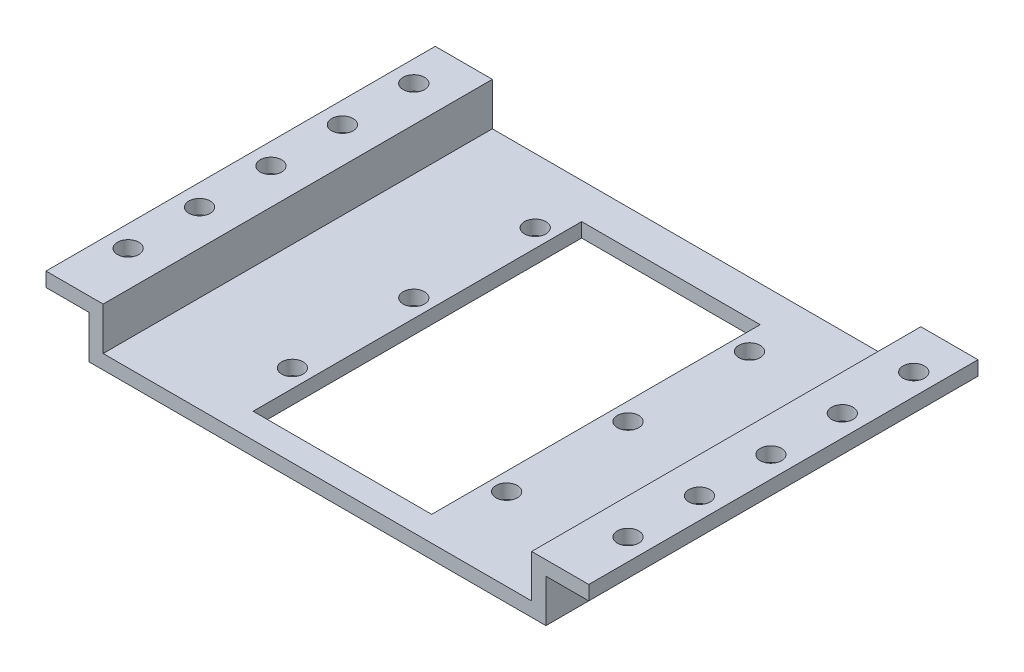
SolidWorks part; units mm, degrees
material "Polyetheretherketone (PEEK)"
ref_plane "Front Plane" through (0, 0, 0) normal (0, 0, 1) x (1, 0, 0)
ref_plane "Top Plane" through (0, 0, 0) normal (0, 1, 0) x (1, 0, 0)
ref_plane "Right Plane" through (0, 0, 0) normal (1, 0, 0) x (0, 0, -1)
sketch "Sketch1" plane through (0, 0, 0) normal (0, 0, 1) x (1, 0, 0)
  line L0 (0, 0) -> (0, 19.6061) construction
  line L1 (12.5, 0) -> (12.5, 2)
  line L2 (32, 0) -> (12.5, 0)
  line L3 (-12.5, 2) -> (-30, 2)
  line L4 (-30, 2) -> (-30, 8)
  line L5 (-30, 8) -> (-38, 8)
  line L6 (-38, 8) -> (-38, 6)
  line L7 (-38, 6) -> (-32, 6)
  line L8 (-32, 6) -> (-32, 0)
  line L9 (-32, 0) -> (-12.5, 0)
  line L10 (-12.5, 0) -> (-12.5, 2)
  line L11 (32, 6) -> (32, 0)
  line L12 (38, 6) -> (32, 6)
  line L13 (38, 8) -> (38, 6)
  line L14 (30, 8) -> (38, 8)
  line L15 (30, 2) -> (30, 8)
  line L16 (12.5, 2) -> (30, 2)
  dimension "D1" = 2
  dimension "D2" = 2
  dimension "D3" = 2
  dimension "D6" = 25
  dimension "D8" = 60
  dimension "D9" = 8
  dimension "D10" = 8
extrude "Boss-Extrude1" add sketch "Sketch1" along normal blind 50
sketch "Sketch2" plane through (0, 2, 0) normal (0, 1, 0) x (1, 0, 0)
  line L0 (-12.5, -50) -> (-30, -50) construction
  line L2 (0, 0) -> (0, -23.6531) construction
  point P0 (-15, -47)
  point P5 (-15, -30)
  point P6 (15, -13)
  point P7 (-15, -13)
  point P8 (15, -30)
  point P12 (15, -47)
  dimension "D1" = 3
  dimension "D2" = 30
  dimension "D3" = 17
  dimension "D4" = 17
hole_wizard "Ø3.0mm Dowel Hole1" positions "Sketch3" profile "Sketch4" hole size "Ø3.0" standard "ANSI Metric" end condition through all
sketch "Sketch3" plane through (0, 2, 0) normal (0, 1, 0) x (1, 0, 0)
  point P0 (-15, -47)
  point P3 (-15, -30)
  point P6 (-15, -13)
  point P10 (15, -13)
  point P13 (15, -30)
  point P16 (15, -47)
sketch "Sketch4" plane through (-15, 2, 47) normal (1, 0, 0) x (0, 0, 1)
  line L0 (0, 0) -> (0, 2)
  line L1 (0, 2) -> (1.5, 2)
  line L2 (1.5, 2) -> (1.5, 0)
  line L5 (1.5, 0) -> (0, 0)
  line L11 (0, -6.35) -> (0, 107.95) construction
  dimension "Thru Hole Dia." = 3
  dimension "Thru Hole Depth" = 2
sketch "Sketch5" plane through (0, 8, 0) normal (0, 1, 0) x (1, 0, 0)
  line L1 (-38, -25) -> (-20.1362, -25) construction
  line L2 (-38, -50) -> (-38, 0) construction
  line L3 (0, 0) -> (0, -25.8286) construction
  point P0 (-35, -30)
  point P1 (-35, -10)
  point P2 (-35, -20)
  point P7 (-35, -40)
  point P8 (35, -30)
  point P9 (35, -25)
  point P10 (35, -20)
  dimension "D1" = 10
  dimension "D2" = 5
  dimension "D3" = 3
  dimension "D4" = 15
hole_wizard "Ø3.0mm Dowel Hole2" positions "Sketch6" profile "Sketch7" hole size "Ø3.0" standard "ANSI Metric" end condition through all
sketch "Sketch6" plane through (0, 8, 0) normal (0, 1, 0) x (1, 0, 0)
  point P0 (-35, -20)
  point P3 (-35, -10)
  point P6 (-35, -30)
  point P19 (-35, -40)
sketch "Sketch7" plane through (-35, 8, 20) normal (1, 0, 0) x (0, 0, 1)
  line L0 (0, 0) -> (0, 8)
  line L1 (0, 8) -> (1.5, 8)
  line L2 (1.5, 8) -> (1.5, 0)
  line L5 (1.5, 0) -> (0, 0)
  line L11 (0, -6.35) -> (0, 107.95) construction
  dimension "Thru Hole Dia." = 3
  dimension "Thru Hole Depth" = 8
sketch "Sketch9" plane through (0, 2, 0) normal (0, 1, 0) x (1, 0, 0)
  line L0 (-12.5, -50) -> (-12.5, 0) construction
  line L1 (12.5, 0) -> (-12.5, 0)
  line L2 (12.5, 0) -> (12.5, -9)
  line L3 (12.5, -9) -> (-12.5, -9)
  line L4 (-12.5, 0) -> (-12.5, -9)
  dimension "D1" = 4
extrude "Boss-Extrude3" add sketch "Sketch9" against normal blind 2
mirror "Mirror1" about plane through (0, 0, 0) normal (1, 0, 0) of "Ø3.0mm Dowel Hole2"
sketch "Sketch10" plane through (0, 8, 0) normal (0, 1, 0) x (1, 0, 0)
  line L0 (-38, -50) -> (-38, 0) construction
  line L1 (38, 0) -> (-38, 0)
  line L2 (38, 0) -> (38, -4)
  line L3 (38, -4) -> (-38, -4)
  line L4 (-38, 0) -> (-38, -4)
  line L5 (-12.5, -9) -> (12.5, -9) construction
  dimension "D1" = 5
extrude "Cut-Extrude1" cut sketch "Sketch10" against normal blind 10
sketch "Sketch12" plane through (0, 0, 50) normal (0, 0, 1) x (1, 0, 0)
  line L0 (32, 0) -> (32, 6) construction
  line L1 (-32, 0) -> (32, 0)
  line L3 (-30, 2) -> (30, 2)
  line L5 (30, 2) -> (12.5, 2) construction
  line L6 (32, 0) -> (32, 6)
  line L7 (32, 6) -> (38, 6) construction
  line L8 (32, 6) -> (38, 6)
  line L9 (38, 6) -> (38, 8)
  line L10 (38, 8) -> (30, 8)
  line L11 (30, 8) -> (30, 2)
  line L12 (-30, 2) -> (-30, 8)
  line L13 (-30, 8) -> (-38, 8)
  line L14 (-38, 8) -> (-38, 6)
  line L15 (-38, 6) -> (-32, 6)
  line L16 (-32, 6) -> (-32, 0)
extrude "Boss-Extrude4" add sketch "Sketch12" along normal blind 8.5
sketch "Sketch13" plane through (0, 2, 0) normal (0, 1, 0) x (1, 0, 0)
  line L0 (-12.5, -50) -> (-12.5, -9) construction
  line L1 (12.5, -50) -> (-12.5, -50)
  line L2 (12.5, -50) -> (12.5, -55)
  line L3 (12.5, -55) -> (-12.5, -55)
  line L4 (-12.5, -50) -> (-12.5, -55)
  dimension "D1" = 5
extrude "Cut-Extrude2" cut sketch "Sketch13" against normal blind 8.5
hole_wizard "Ø3.0mm Dowel Hole3" positions "Sketch14" profile "Sketch15" hole size "Ø3.0" standard "ANSI Metric" end condition through all
sketch "Sketch14" plane through (0, 8, 0) normal (0, 1, 0) x (1, 0, 0)
  point P0 (35, -50)
  point P3 (-35, -50)
sketch "Sketch15" plane through (35, 8, 50) normal (1, 0, 0) x (0, 0, 1)
  line L0 (0, 0) -> (0, 8)
  line L1 (0, 8) -> (1.5, 8)
  line L2 (1.5, 8) -> (1.5, 0)
  line L5 (1.5, 0) -> (0, 0)
  line L11 (0, -6.35) -> (0, 107.95) construction
  dimension "Thru Hole Dia." = 3
  dimension "Thru Hole Depth" = 8
